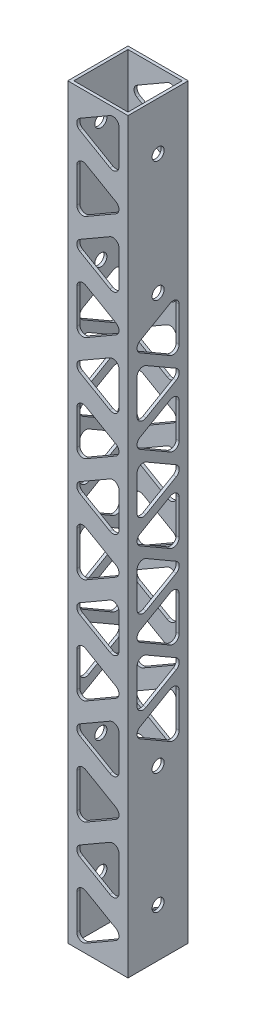
SolidWorks part; units mm, degrees
material "6061 Alloy"
ref_plane "Front Plane" through (0, 0, 0) normal (0, 0, 1) x (1, 0, 0)
ref_plane "Top Plane" through (0, 0, 0) normal (0, 1, 0) x (1, 0, 0)
ref_plane "Right Plane" through (0, 0, 0) normal (1, 0, 0) x (0, 0, -1)
sketch "Sketch1" plane through (0, 0, 0) normal (0, 1, 0) x (1, 0, 0)
  line L0 (-31.75, -31.75) -> (31.75, 31.75) construction
  line L1 (-31.75, 31.75) -> (31.75, 31.75)
  line L2 (-31.75, 31.75) -> (-31.75, -31.75)
  line L3 (-31.75, -31.75) -> (31.75, -31.75)
  line L4 (31.75, 31.75) -> (31.75, -31.75)
  line L5 (28.575, -28.575) -> (-28.575, 28.575) construction
  line L6 (-28.575, 28.575) -> (28.575, 28.575)
  line L7 (-28.575, 28.575) -> (-28.575, -28.575)
  line L8 (-28.575, -28.575) -> (28.575, -28.575)
  line L9 (28.575, 28.575) -> (28.575, -28.575)
  point P7 (0, 0)
  point P10 (0, 0)
  point P14 (0, 0)
  dimension "D1" = 63.5
  dimension "D2" = 3.175
  dimension "D3" = 3.175
  dimension "D4" = 3.175
extrude "Boss-Extrude1" add sketch "Sketch1" along normal blind 787.4
sketch "Sketch2" plane through (-31.75, 0, 0) normal (-1, 0, 0) x (0, 0, 1)
  line L0 (31.75, 393.7) -> (-31.75, 393.7) construction
  line L1 (31.75, 787.4) -> (31.75, 0) construction
  line L2 (-31.75, 787.4) -> (-31.75, 0) construction
  line L3 (0, 50.8) -> (0, 736.6) construction
  line L4 (0, 609.6) -> (0, 177.8) construction
  circle A0 centre (0, 50.8) radius 6.35
  circle A1 centre (0, 177.8) radius 6.35
  circle A2 centre (0, 609.6) radius 6.35
  circle A3 centre (0, 736.6) radius 6.35
  point P10 (0, 393.7)
  point P13 (0, 393.7)
  dimension "D3" = 12.7
extrude "Cut-Extrude1" cut sketch "Sketch2" against normal through all
sketch "Sketch3" plane through (31.75, 0, 0) normal (1, 0, 0) x (0, 0, -1)
  line L0 (31.75, 787.4) -> (31.75, 0) construction
  line L1 (-19.05, 212.0059) -> (12.7, 193.675)
  line L2 (22.225, 199.1743) -> (22.225, 235.836)
  line L3 (12.7, 241.3353) -> (-19.05, 223.0044)
  line L4 (19.05, 266.9985) -> (-12.7, 285.3294)
  line L5 (-22.225, 279.8301) -> (-22.225, 243.1684)
  line L6 (-12.7, 237.6691) -> (19.05, 256)
  line L7 (-31.75, 787.4) -> (-31.75, 0) construction
  line L8 (-19.05, 300.1033) -> (12.7, 281.7724)
  line L9 (22.225, 287.2717) -> (22.225, 323.9334)
  line L10 (12.7, 329.4327) -> (-19.05, 311.1018)
  line L11 (19.05, 355.0959) -> (-12.7, 373.4268)
  line L12 (-22.225, 367.9275) -> (-22.225, 331.2658)
  line L13 (-12.7, 325.7665) -> (19.05, 344.0974)
  line L14 (-19.05, 388.2007) -> (12.7, 369.8699)
  line L15 (22.225, 375.3691) -> (22.225, 412.0309)
  line L16 (12.7, 417.5301) -> (-19.05, 399.1993)
  line L17 (19.05, 443.1934) -> (-12.7, 461.5242)
  line L18 (-22.225, 456.025) -> (-22.225, 419.3632)
  line L19 (-12.7, 413.864) -> (19.05, 432.1948)
  line L20 (-19.05, 476.2982) -> (12.7, 457.9673)
  line L21 (22.225, 463.4666) -> (22.225, 500.1283)
  line L22 (12.7, 505.6276) -> (-19.05, 487.2967)
  line L23 (19.05, 531.2908) -> (-12.7, 549.6217)
  line L24 (-22.225, 544.1224) -> (-22.225, 507.4607)
  line L25 (-12.7, 501.9614) -> (19.05, 520.2923)
  line L26 (-19.05, 564.3956) -> (12.7, 546.0647)
  line L27 (22.225, 551.564) -> (22.225, 588.2257)
  line L28 (12.7, 593.725) -> (-19.05, 575.3941)
  line L32 (-12.7, 590.0588) -> (19.05, 608.3897) [skipped]
  line L33 (-22.225, 632.2198) -> (-22.225, 595.5581) [skipped]
  line L34 (19.05, 619.3882) -> (-12.7, 637.7191) [skipped]
  circle A0 centre (5.2917, 217.5051) radius 16.9333 construction
  circle A1 centre (-5.2917, 261.4992) radius 16.9333 construction
  arc A2 (-12.7, 285.3294) -> (-22.225, 279.8301) centre (-15.875, 279.8301) ccw
  arc A3 (-22.225, 243.1684) -> (-12.7, 237.6691) centre (-15.875, 243.1684) ccw
  arc A4 (19.05, 266.9985) -> (19.05, 256) centre (15.875, 261.4992) cw
  arc A5 (22.225, 235.836) -> (12.7, 241.3353) centre (15.875, 235.836) ccw
  arc A6 (12.7, 193.675) -> (22.225, 199.1743) centre (15.875, 199.1743) ccw
  arc A7 (-19.05, 212.0059) -> (-19.05, 223.0044) centre (-15.875, 217.5051) cw
  circle A8 centre (0, 177.8) radius 6.35 construction
  arc A9 (-19.05, 300.1033) -> (-19.05, 311.1018) centre (-15.875, 305.6026) cw
  arc A10 (12.7, 281.7724) -> (22.225, 287.2717) centre (15.875, 287.2717) ccw
  arc A11 (22.225, 323.9334) -> (12.7, 329.4327) centre (15.875, 323.9334) ccw
  arc A12 (19.05, 355.0959) -> (19.05, 344.0974) centre (15.875, 349.5967) cw
  arc A13 (-12.7, 373.4268) -> (-22.225, 367.9275) centre (-15.875, 367.9275) ccw
  arc A14 (-22.225, 331.2658) -> (-12.7, 325.7665) centre (-15.875, 331.2658) ccw
  arc A15 (-19.05, 388.2007) -> (-19.05, 399.1993) centre (-15.875, 393.7) cw
  arc A16 (12.7, 369.8699) -> (22.225, 375.3691) centre (15.875, 375.3691) ccw
  arc A17 (22.225, 412.0309) -> (12.7, 417.5301) centre (15.875, 412.0309) ccw
  arc A18 (19.05, 443.1934) -> (19.05, 432.1948) centre (15.875, 437.6941) cw
  arc A19 (-12.7, 461.5242) -> (-22.225, 456.025) centre (-15.875, 456.025) ccw
  arc A20 (-22.225, 419.3632) -> (-12.7, 413.864) centre (-15.875, 419.3632) ccw
  arc A21 (-19.05, 476.2982) -> (-19.05, 487.2967) centre (-15.875, 481.7974) cw
  arc A22 (12.7, 457.9673) -> (22.225, 463.4666) centre (15.875, 463.4666) ccw
  arc A23 (22.225, 500.1283) -> (12.7, 505.6276) centre (15.875, 500.1283) ccw
  arc A24 (19.05, 531.2908) -> (19.05, 520.2923) centre (15.875, 525.7915) cw
  arc A25 (-12.7, 549.6217) -> (-22.225, 544.1224) centre (-15.875, 544.1224) ccw
  arc A26 (-22.225, 507.4607) -> (-12.7, 501.9614) centre (-15.875, 507.4607) ccw
  arc A27 (-19.05, 564.3956) -> (-19.05, 575.3941) centre (-15.875, 569.8949) cw
  arc A28 (12.7, 546.0647) -> (22.225, 551.564) centre (15.875, 551.564) ccw
  arc A29 (22.225, 588.2257) -> (12.7, 593.725) centre (15.875, 588.2257) ccw
  circle A33 centre (0, 609.6) radius 6.35 construction
  arc A34 (-22.225, 595.5581) -> (-12.7, 590.0588) centre (-15.875, 595.5581) ccw [skipped]
  arc A35 (-12.7, 637.7191) -> (-22.225, 632.2198) centre (-15.875, 632.2198) ccw [skipped]
  arc A36 (19.05, 619.3882) -> (19.05, 608.3897) centre (15.875, 613.889) cw [skipped]
  point P24 (-22.225, 217.5051)
  point P27 (22.225, 261.4992)
  point P104 (0, 0)
  dimension "D1" = 6.35
  dimension "D7" = 15.875
  dimension "D2" = 9.525
  dimension "D3" = 9.525
  dimension "D4" = 9.525
  dimension "D5" = 9.525
  dimension "D6" = 9.525
  dimension "D9" = 15.875
  dimension "D8" = 5
extrude "Cut-Extrude2" cut sketch "Sketch3" against normal blind 71.12
sketch "Sketch5" plane through (0, 0, -31.75) normal (0, 0, -1) x (-1, 0, 0)
  line L1 (19.05, 759.5441) -> (-12.7, 777.875)
  line L2 (-22.225, 772.3757) -> (-22.225, 735.714)
  line L3 (-12.7, 730.2147) -> (19.05, 748.5456)
  line L4 (-19.05, 691.3603) -> (12.7, 673.0295)
  line L5 (22.225, 678.5287) -> (22.225, 715.1905)
  line L6 (12.7, 720.6897) -> (-19.05, 702.3589)
  line L7 (-31.75, 787.4) -> (-31.75, 0) construction
  line L8 (-31.75, 787.4) -> (31.75, 787.4) construction
  line L9 (31.75, 787.4) -> (31.75, 0) construction
  line L10 (19.05, 648.9601) -> (-12.7, 667.2909)
  line L11 (-22.225, 661.7917) -> (-22.225, 625.1299)
  line L12 (-12.7, 619.6307) -> (19.05, 637.9615)
  line L13 (-19.05, 580.7763) -> (12.7, 562.4454)
  line L14 (22.225, 567.9447) -> (22.225, 604.6064)
  line L15 (12.7, 610.1057) -> (-19.05, 591.7748)
  line L16 (19.05, 538.376) -> (-12.7, 556.7068)
  line L17 (-22.225, 551.2076) -> (-22.225, 514.5458)
  line L18 (-12.7, 509.0466) -> (19.05, 527.3774)
  line L19 (-19.05, 470.1922) -> (12.7, 451.8613)
  line L20 (22.225, 457.3606) -> (22.225, 494.0223)
  line L21 (12.7, 499.5216) -> (-19.05, 481.1907)
  line L22 (19.05, 427.7919) -> (-12.7, 446.1228)
  line L23 (-22.225, 440.6235) -> (-22.225, 403.9618)
  line L24 (-12.7, 398.4625) -> (19.05, 416.7934)
  line L25 (-19.05, 359.6081) -> (12.7, 341.2772)
  line L26 (22.225, 346.7765) -> (22.225, 383.4382)
  line L27 (12.7, 388.9375) -> (-19.05, 370.6066)
  line L28 (19.05, 317.2078) -> (-12.7, 335.5387)
  line L29 (-22.225, 330.0394) -> (-22.225, 293.3777)
  line L30 (-12.7, 287.8784) -> (19.05, 306.2093)
  line L31 (-19.05, 249.024) -> (12.7, 230.6932)
  line L32 (22.225, 236.1924) -> (22.225, 272.8542)
  line L33 (12.7, 278.3534) -> (-19.05, 260.0226)
  line L34 (19.05, 206.6237) -> (-12.7, 224.9546)
  line L35 (-22.225, 219.4553) -> (-22.225, 182.7936)
  line L36 (-12.7, 177.2943) -> (19.05, 195.6252)
  line L37 (-19.05, 138.4399) -> (12.7, 120.1091)
  line L38 (22.225, 125.6083) -> (22.225, 162.2701)
  line L39 (12.7, 167.7693) -> (-19.05, 149.4385)
  line L40 (19.05, 96.0397) -> (-12.7, 114.3705)
  line L41 (-22.225, 108.8713) -> (-22.225, 72.2095)
  line L42 (-12.7, 66.7103) -> (19.05, 85.0411)
  line L43 (-19.05, 27.8559) -> (12.7, 9.525)
  line L44 (22.225, 15.0243) -> (22.225, 51.686)
  line L45 (12.7, 57.1853) -> (-19.05, 38.8544)
  line L46 (-31.75, 0) -> (31.75, 0) construction
  circle A0 centre (-5.2917, 754.0449) radius 16.9333 construction
  circle A1 centre (5.2917, 696.8596) radius 16.9333 construction
  arc A2 (22.225, 715.1905) -> (12.7, 720.6897) centre (15.875, 715.1905) ccw
  arc A3 (12.7, 673.0295) -> (22.225, 678.5287) centre (15.875, 678.5287) ccw
  arc A4 (-19.05, 691.3603) -> (-19.05, 702.3589) centre (-15.875, 696.8596) cw
  arc A5 (-22.225, 735.714) -> (-12.7, 730.2147) centre (-15.875, 735.714) ccw
  arc A6 (-12.7, 777.875) -> (-22.225, 772.3757) centre (-15.875, 772.3757) ccw
  arc A7 (19.05, 759.5441) -> (19.05, 748.5456) centre (15.875, 754.0449) cw
  arc A8 (19.05, 648.9601) -> (19.05, 637.9615) centre (15.875, 643.4608) cw
  arc A9 (-12.7, 667.2909) -> (-22.225, 661.7917) centre (-15.875, 661.7917) ccw
  arc A10 (-22.225, 625.1299) -> (-12.7, 619.6307) centre (-15.875, 625.1299) ccw
  arc A11 (-19.05, 580.7763) -> (-19.05, 591.7748) centre (-15.875, 586.2755) cw
  arc A12 (12.7, 562.4454) -> (22.225, 567.9447) centre (15.875, 567.9447) ccw
  arc A13 (22.225, 604.6064) -> (12.7, 610.1057) centre (15.875, 604.6064) ccw
  arc A14 (19.05, 538.376) -> (19.05, 527.3774) centre (15.875, 532.8767) cw
  arc A15 (-12.7, 556.7068) -> (-22.225, 551.2076) centre (-15.875, 551.2076) ccw
  arc A16 (-22.225, 514.5458) -> (-12.7, 509.0466) centre (-15.875, 514.5458) ccw
  arc A17 (-19.05, 470.1922) -> (-19.05, 481.1907) centre (-15.875, 475.6914) cw
  arc A18 (12.7, 451.8613) -> (22.225, 457.3606) centre (15.875, 457.3606) ccw
  arc A19 (22.225, 494.0223) -> (12.7, 499.5216) centre (15.875, 494.0223) ccw
  arc A20 (19.05, 427.7919) -> (19.05, 416.7934) centre (15.875, 422.2926) cw
  arc A21 (-12.7, 446.1228) -> (-22.225, 440.6235) centre (-15.875, 440.6235) ccw
  arc A22 (-22.225, 403.9618) -> (-12.7, 398.4625) centre (-15.875, 403.9618) ccw
  arc A23 (-19.05, 359.6081) -> (-19.05, 370.6066) centre (-15.875, 365.1074) cw
  arc A24 (12.7, 341.2772) -> (22.225, 346.7765) centre (15.875, 346.7765) ccw
  arc A25 (22.225, 383.4382) -> (12.7, 388.9375) centre (15.875, 383.4382) ccw
  arc A26 (19.05, 317.2078) -> (19.05, 306.2093) centre (15.875, 311.7086) cw
  arc A27 (-12.7, 335.5387) -> (-22.225, 330.0394) centre (-15.875, 330.0394) ccw
  arc A28 (-22.225, 293.3777) -> (-12.7, 287.8784) centre (-15.875, 293.3777) ccw
  arc A29 (-19.05, 249.024) -> (-19.05, 260.0226) centre (-15.875, 254.5233) cw
  arc A30 (12.7, 230.6932) -> (22.225, 236.1924) centre (15.875, 236.1924) ccw
  arc A31 (22.225, 272.8542) -> (12.7, 278.3534) centre (15.875, 272.8542) ccw
  arc A32 (19.05, 206.6237) -> (19.05, 195.6252) centre (15.875, 201.1245) cw
  arc A33 (-12.7, 224.9546) -> (-22.225, 219.4553) centre (-15.875, 219.4553) ccw
  arc A34 (-22.225, 182.7936) -> (-12.7, 177.2943) centre (-15.875, 182.7936) ccw
  arc A35 (-19.05, 138.4399) -> (-19.05, 149.4385) centre (-15.875, 143.9392) cw
  arc A36 (12.7, 120.1091) -> (22.225, 125.6083) centre (15.875, 125.6083) ccw
  arc A37 (22.225, 162.2701) -> (12.7, 167.7693) centre (15.875, 162.2701) ccw
  arc A38 (19.05, 96.0397) -> (19.05, 85.0411) centre (15.875, 90.5404) cw
  arc A39 (-12.7, 114.3705) -> (-22.225, 108.8713) centre (-15.875, 108.8713) ccw
  arc A40 (-22.225, 72.2095) -> (-12.7, 66.7103) centre (-15.875, 72.2095) ccw
  arc A41 (-19.05, 27.8559) -> (-19.05, 38.8544) centre (-15.875, 33.3551) cw
  arc A42 (12.7, 9.525) -> (22.225, 15.0243) centre (15.875, 15.0243) ccw
  arc A43 (22.225, 51.686) -> (12.7, 57.1853) centre (15.875, 51.686) ccw
  point P22 (22.225, 754.0449)
  point P30 (-22.225, 696.8596)
  dimension "D1" = 6.35
  dimension "D2" = 9.525
  dimension "D3" = 9.525
  dimension "D4" = 9.525
  dimension "D5" = 9.525
  dimension "D6" = 9.525
  dimension "D7" = 9.525
  dimension "D9" = 9.525
  dimension "D8" = 7
extrude "Cut-Extrude3" cut sketch "Sketch5" against normal blind 71.12
equation "\"D1@Boss-Extrude1\"=\"HoleDist\"+4"
